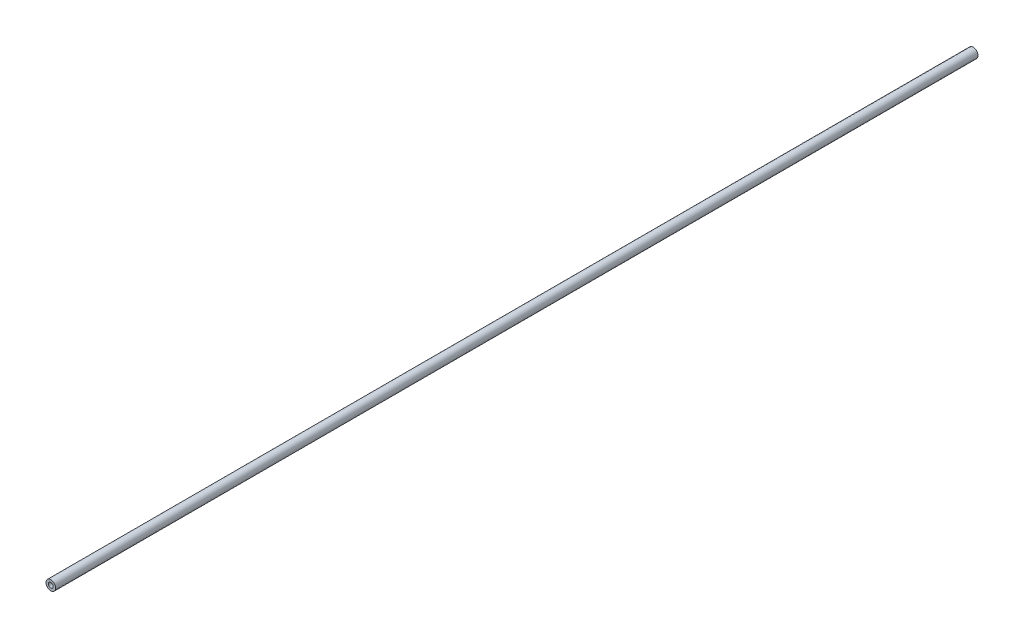
SolidWorks part; units mm, degrees
ref_plane "Front Plane" through (0, 0, 0) normal (0, 0, 1) x (1, 0, 0)
ref_plane "Top Plane" through (0, 0, 0) normal (0, 1, 0) x (1, 0, 0)
ref_plane "Right Plane" through (0, 0, 0) normal (1, 0, 0) x (0, 0, -1)
sketch "Sketch2" plane through (0, 0, 0) normal (0, 0, 1) x (1, 0, 0)
  circle A0 centre (0, 0) radius 2.54
  circle A1 centre (0, 0) radius 1.27
  dimension "D1" = 5.08
  dimension "D2" = 2.54
extrude "Boss-Extrude1" add sketch "Sketch2" along normal blind 485.14
